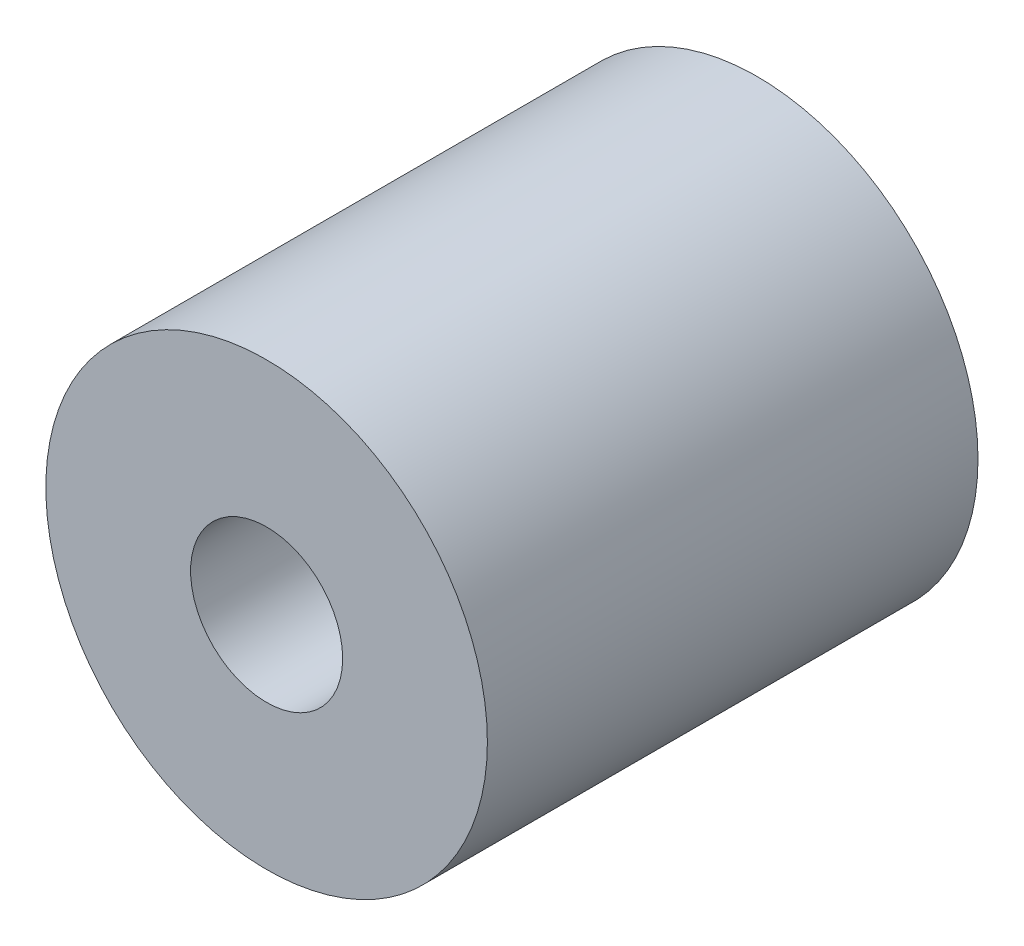
SolidWorks part; units mm, degrees
ref_plane "Front Plane" through (0, 0, 0) normal (0, 0, 1) x (1, 0, 0)
ref_plane "Top Plane" through (0, 0, 0) normal (0, 1, 0) x (1, 0, 0)
ref_plane "Right Plane" through (0, 0, 0) normal (1, 0, 0) x (0, 0, -1)
sketch "Sketch1" plane through (0, 0, 0) normal (0, 0, 1) x (1, 0, 0)
  circle A0 centre (0, 0) radius 1.55
  circle A1 centre (0, 0) radius 4.5
  dimension "D1" = 3.1
  dimension "D2" = 9
extrude "Boss-Extrude1" add sketch "Sketch1" along normal blind 10
